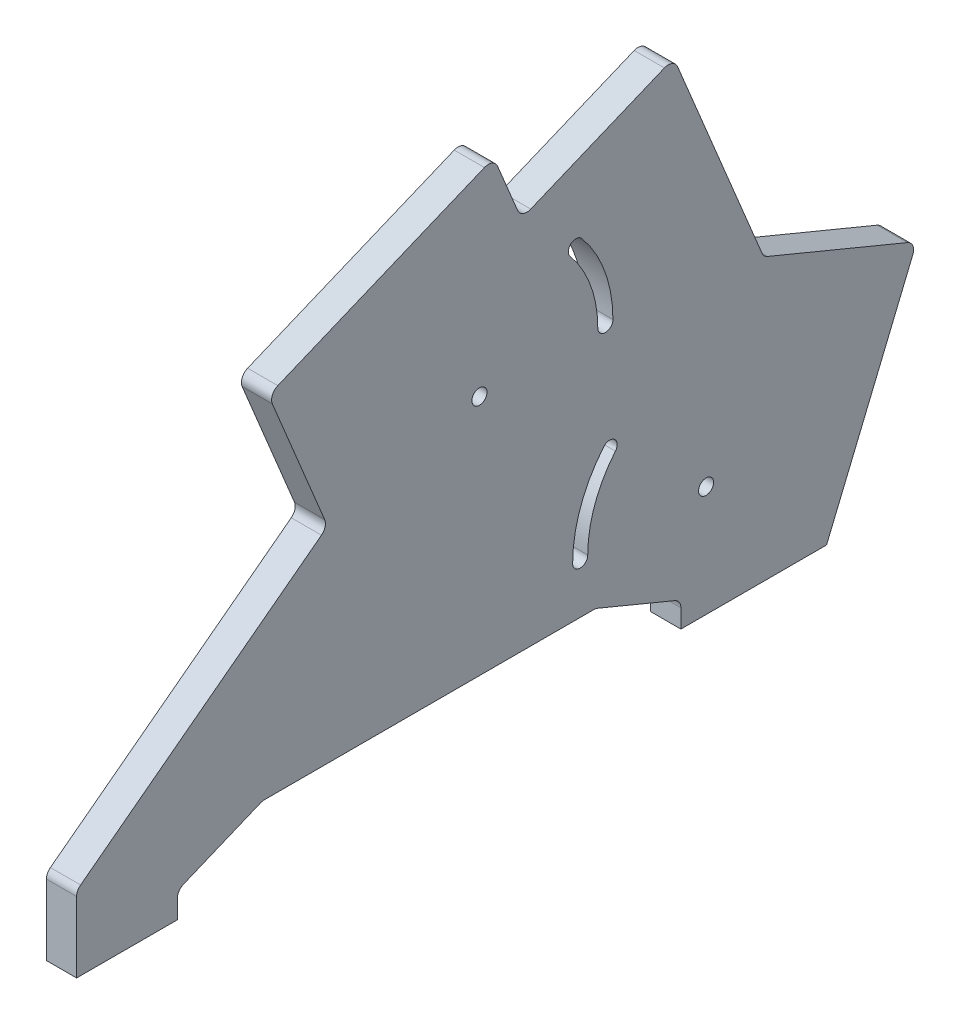
SolidWorks part; units mm, degrees
material "1060 Alloy"
ref_plane "Front Plane" through (0, 0, 0) normal (0, 0, 1) x (1, 0, 0)
ref_plane "Top Plane" through (0, 0, 0) normal (0, 1, 0) x (1, 0, 0)
ref_plane "Right Plane" through (0, 0, 0) normal (1, 0, 0) x (0, 0, -1)
sketch "Sketch1" plane through (0, 0, 0) normal (1, 0, 0) x (0, 0, -1)
  line L0 (0, 0) -> (0, 15)
  line L1 (38.8897, 80.8553) -> (54.5797, 42.9762) construction
  line L2 (38.8897, 80.8553) -> (112.8001, 111.47) construction
  line L3 (54.5797, 42.9762) -> (128.4901, 73.5909) construction
  line L5 (112.8001, 111.47) -> (128.4901, 73.5909) construction
  line L6 (20, 5) -> (20, 0)
  line L7 (0, 0) -> (20, 0)
  line L10 (80, 60) -> (105, 60) construction
  line L11 (99.1511, 76.0697) -> (80, 60) construction
  line L12 (100, 22) -> (125, 22) construction
  line L13 (125, 22) -> (105.8489, 38.0697) construction
  line L14 (166.1103, 42.8553) -> (150.4203, 4.9762) construction
  line L15 (166.1103, 42.8553) -> (92.1999, 73.47) construction
  line L16 (150.4203, 4.9762) -> (76.5099, 35.5909) construction
  line L17 (92.1999, 73.47) -> (76.5099, 35.5909) construction
  line L19 (166.8247, 43.2195) -> (136.4285, 55.81)
  line L20 (38.1102, 81.1261) -> (82.8344, 99.6514)
  line L21 (82.8344, 99.6514) -> (88.3305, 86.3826)
  line L22 (38.1102, 81.1261) -> (49.8545, 52.7728)
  line L23 (49.8545, 52.7728) -> (0, 15)
  line L24 (88.3305, 86.3826) -> (118.5757, 98.9106)
  line L25 (118.5757, 98.9106) -> (136.4285, 55.81)
  line L43 (148.9226, 0) -> (120, 0)
  line L56 (120, 5) -> (120, 0)
  line L58 (20, 5) -> (36.8995, 12)
  line L59 (36.8995, 12) -> (103.1005, 12)
  line L60 (103.1005, 12) -> (120, 5)
  line L61 (148.9226, 0) -> (166.8247, 43.2195)
  line L63 (174.6584, 100) -> (-14.1241, 100) construction
  circle A0 centre (80, 60) radius 1.5
  circle A1 centre (125, 22) radius 1.5
  arc A2 (99.1511, 76.0697) -> (105, 60) centre (80, 60) cw construction
  arc A3 (106.5, 60) -> (100.3002, 77.0339) centre (80, 60) ccw
  arc A4 (103.5, 60) -> (98.002, 75.1055) centre (80, 60) ccw
  arc A5 (103.5, 60) -> (106.5, 60) centre (105, 60) ccw
  arc A6 (100.3002, 77.0339) -> (98.002, 75.1055) centre (99.1511, 76.0697) ccw
  arc A7 (105.8489, 38.0697) -> (100, 22) centre (125, 22) ccw construction
  arc A8 (104.6998, 39.0339) -> (98.5, 22) centre (125, 22) ccw
  arc A9 (106.998, 37.1055) -> (101.5, 22) centre (125, 22) ccw
  arc A10 (106.998, 37.1055) -> (104.6998, 39.0339) centre (105.8489, 38.0697) ccw
  arc A11 (98.5, 22) -> (101.5, 22) centre (100, 22) ccw
  point P17 (103.4923, 68.5505)
  point P22 (101.5077, 30.5505)
  dimension "D1" = 3
  dimension "D3" = 1.5
  dimension "D8" = 15
  dimension "D11" = 22
  dimension "D12" = 80
  dimension "D14" = 10
  dimension "D17" = 6
  dimension "D21" = 30
  dimension "D22" = 35
  dimension "D23" = 80
  dimension "D18" = 6
  dimension "D29" = 60
  dimension "D2" = 25
  dimension "D4" = 25
  dimension "D5" = 40
  dimension "D6" = 40
  dimension "D7" = 125
  dimension "D9" = 20
  dimension "D10" = 100
  dimension "D13" = 5
  dimension "D20" = 30
  dimension "D31" = 22.5
  dimension "D32" = 100
  dimension "D33" = 22.5
extrude "Boss-Extrude1" add sketch "Sketch1" along normal blind 6
fillet "Fillet1" radius 2 12 edges at (3, 12, -36.8995) (3, 5, -20) (3, 12, -103.1005) (3, 43.2195, -166.8247) (3, 55.81, -136.4285) (3, 98.9106, -118.5757) (3, 86.3826, -88.3305) (3, 99.6514, -82.8344) (3, 81.1261, -38.1102) (3, 52.7728, -49.8545) (3, 15, 0) (3, 5, -120)
hole_wizard "Tap Drill for M3 Tap1" positions "Sketch3" profile "Sketch2" hole size "M3" standard "ISO"
sketch "Sketch3" plane through (0, 0, 0) normal (0, -1, 0) x (-1, 0, 0)
  line L0 (-6, 20) -> (0, 20) construction
  line L1 (0, 0) -> (0, 20) construction
  line L2 (-6, 120) -> (0, 120) construction
  point P0 (-3, 10)
  point P2 (-3, 130)
  dimension "D1" = 10
  dimension "D2" = 3
  dimension "D3" = 10
sketch "Sketch2" plane through (3, 0, -10) normal (1, 0, 0) x (0, 0, -1)
  line L0 (0, 0) -> (0, 10.7511)
  line L1 (0, 10.7511) -> (1.25, 10)
  line L2 (1.25, 10) -> (1.25, 0)
  line L5 (1.25, 0) -> (0, 0)
  line L10 (0, 10.7511) -> (-1.25, 10) construction
  line L11 (0, -6.35) -> (0, 107.95) construction
  dimension "Hole Dia." = 2.5
  dimension "Hole Depth" = 10
  dimension "Drill Angle" = 118
equation "\"ˇ35\"=76.24"
